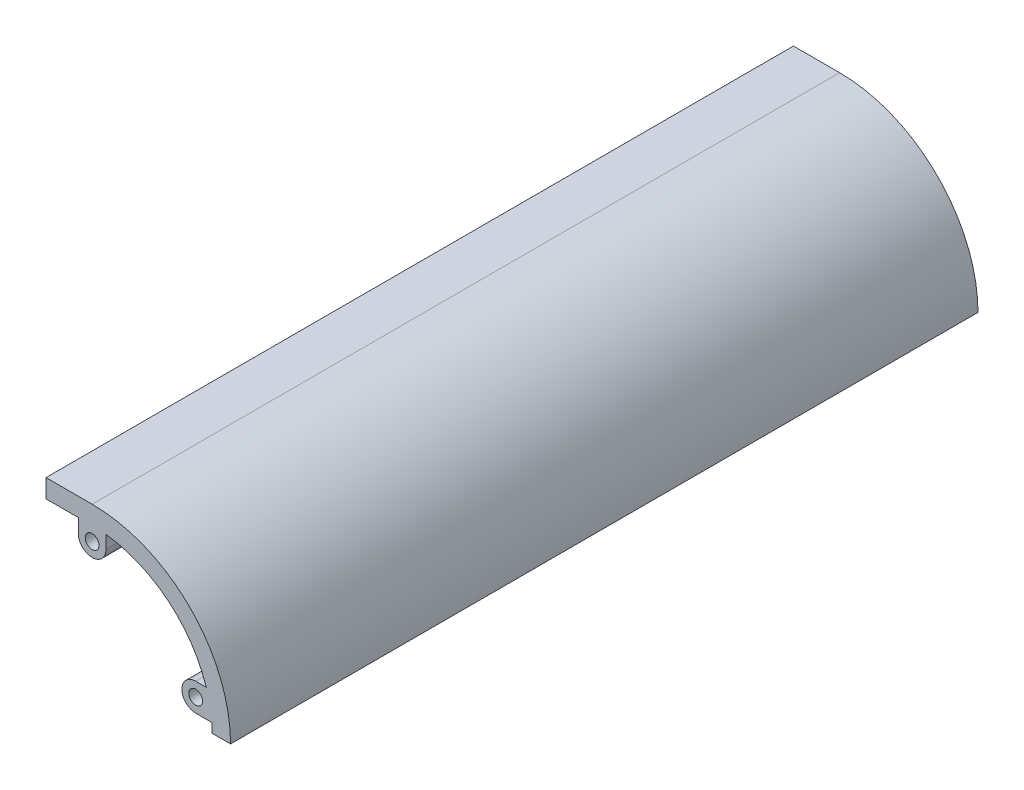
SolidWorks part; units mm, degrees
ref_plane "前视基准面" through (0, 0, 0) normal (0, 0, 1) x (1, 0, 0)
ref_plane "上视基准面" through (0, 0, 0) normal (0, 1, 0) x (1, 0, 0)
ref_plane "右视基准面" through (0, 0, 0) normal (1, 0, 0) x (0, 0, -1)
sketch "草图1" plane through (0, 0, 0) normal (0, 0, 1) x (1, 0, 0)
  line L0 (-6.3158, 9.3947) -> (-6.3158, 12.3947)
  line L1 (-13.3158, 16.3947) -> (-3.3158, 16.3947)
  line L2 (-13.3158, 16.3947) -> (-13.3158, 12.3947)
  line L3 (22.6842, -13.6053) -> (26.6842, -13.6053)
  line L7 (-13.3158, 12.3947) -> (-6.3158, 12.3947)
  line L9 (-0.3158, 9.3947) -> (-0.3158, 12.2211)
  line L10 (19.1342, -5.6053) -> (21.4228, -5.6053)
  line L11 (19.1342, -11.6053) -> (22.6072, -11.6053)
  arc A0 (22.6842, -13.6053) -> (22.6072, -11.6053) centre (-3.3158, -13.6053) ccw
  arc A1 (26.6842, -13.6053) -> (-3.3158, 16.3947) centre (-3.3158, -13.6053) ccw
  arc A2 (-6.3158, 9.3947) -> (-0.3158, 9.3947) centre (-3.3158, 9.3947) ccw
  circle A3 centre (-3.3158, 9.3947) radius 1.5
  arc A4 (19.1342, -5.6053) -> (19.1342, -11.6053) centre (19.1342, -8.6053) ccw
  circle A5 centre (19.1342, -8.6053) radius 1.5
  arc A6 (21.4228, -5.6053) -> (-0.3158, 12.2211) centre (-3.3158, -13.6053) ccw
  dimension "D5" = 52
  dimension "D2" = 6
  dimension "D3" = 3
  dimension "D6" = 6
  dimension "D7" = 3
  dimension "D8" = 5
  dimension "D1" = 4
  dimension "D4" = 30
extrude "凸台-拉伸1" add sketch "草图1" along normal blind 162
ref_plane "基准面1" through (0, 0, 81) normal (0, 0, 1) x (1, 0, 0)
sketch "草图3" plane through (0, 0, 81) normal (0, 0, 1) x (1, 0, 0)
  line L0 (-3.3158, 12.3947) -> (-13.3158, 12.3947)
  line L1 (-13.3158, 12.3947) -> (-18.7287, 7.3337)
  arc A1 (-18.7287, 7.3337) -> (-3.3158, 12.3947) centre (-3.3158, -13.6053) ccw
extrude "切除-拉伸1" cut sketch "草图3" against normal mid plane 152
